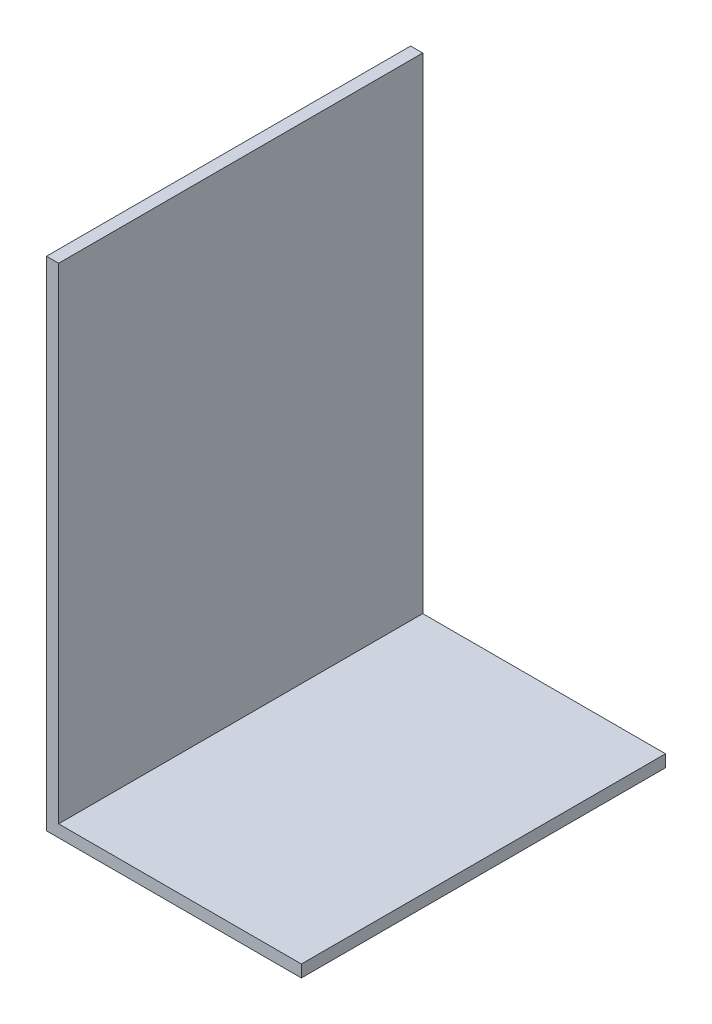
SolidWorks part; units mm, degrees
ref_plane "Front Plane" through (0, 0, 0) normal (0, 0, 1) x (1, 0, 0)
ref_plane "Top Plane" through (0, 0, 0) normal (0, 1, 0) x (1, 0, 0)
ref_plane "Right Plane" through (0, 0, 0) normal (1, 0, 0) x (0, 0, -1)
sketch "Sketch1" plane through (0, 0, 0) normal (0, 0, 1) x (1, 0, 0)
  line L0 (0, 40) -> (0, 0)
  line L1 (0, 0) -> (20, 0)
  dimension "D1" = 40
  dimension "D2" = 20
extrude "Extrude-Thin1" add sketch "Sketch1" along normal mid plane 30 thin
